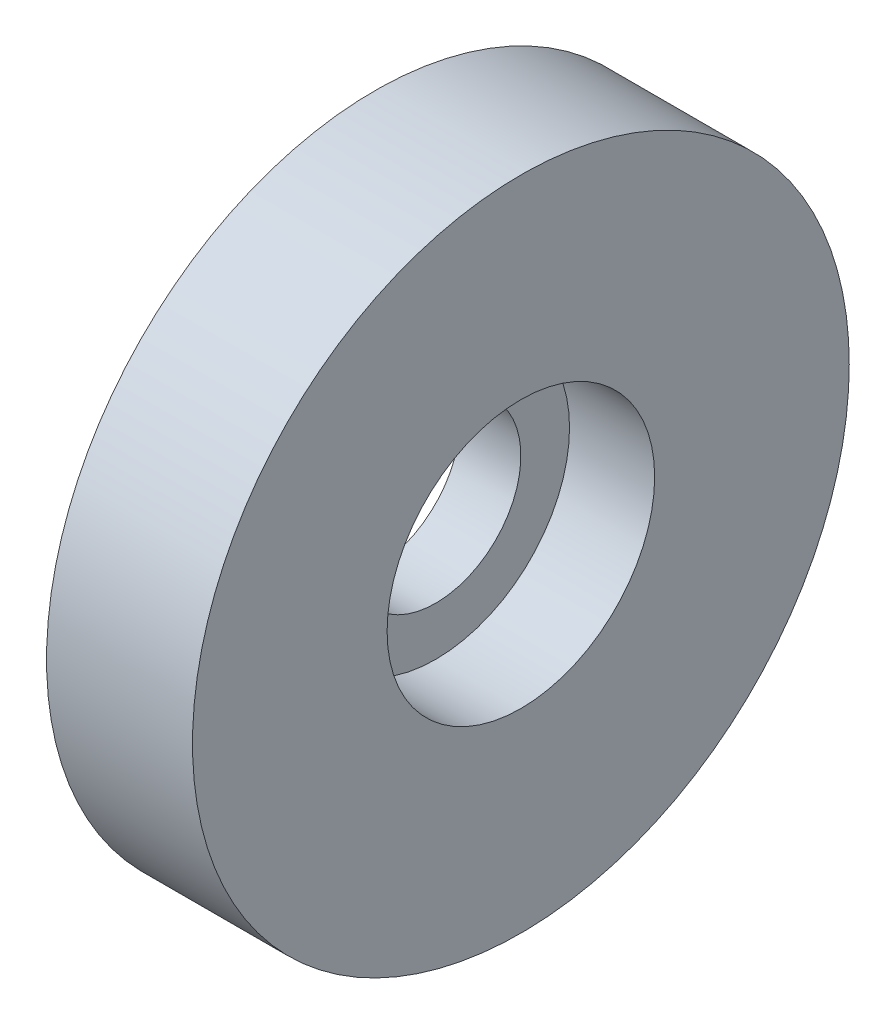
SolidWorks part; units mm, degrees
ref_plane "Front Plane" through (0, 0, 0) normal (0, 0, 1) x (1, 0, 0)
ref_plane "Top Plane" through (0, 0, 0) normal (0, 1, 0) x (1, 0, 0)
ref_plane "Right Plane" through (0, 0, 0) normal (1, 0, 0) x (0, 0, -1)
sketch "Sketch1" plane through (0, 0, 0) normal (0, 0, 1) x (1, 0, 0)
  line L0 (0, 0) -> (0, -12.5562) construction
  line L1 (-5, 0) -> (5, 0)
  line L2 (5, 0) -> (5, -4)
  line L3 (5, -4) -> (12, -4)
  line L4 (12, -4) -> (16.4979, -15.1251)
  line L5 (16.4979, -15.1251) -> (13, -20)
  line L6 (13, -20) -> (-13, -20)
  line L7 (-16.4979, -15.1251) -> (-13, -20)
  line L8 (-12, -4) -> (-16.4979, -15.1251)
  line L9 (-5, -4) -> (-12, -4)
  line L10 (-5, 0) -> (-5, -4)
  line L11 (0, 7) -> (15.343, 7) construction
  point P14 (0, -20)
  point P18 (0, 0)
  dimension "D1" = 5
  dimension "D2" = 7
  dimension "D3" = 4
  dimension "D4" = 12
  dimension "D5" = 6
  dimension "D6" = 13
  dimension "D7" = 20
  dimension "D8" = 7
revolve "Revolve1" add sketch "Sketch1" angle 360 about L11
ref_plane "Plane1" through (16.4979, 0, 0) normal (1, 0, 0) x (0, 0, -1)
other "SurfaceCut1"
ref_plane "Plane2" through (12, 0, 0) normal (1, 0, 0) x (0, 0, -1)
sketch "Sketch3" plane through (12, 0, 0) normal (1, 0, 0) x (0, 0, -1)
  line L1 (-30.8206, 37.7451) -> (28.7828, 37.7451)
  line L2 (-30.8206, 37.7451) -> (-30.8206, -21.8582)
  line L3 (-30.8206, -21.8582) -> (28.7828, -21.8582)
  line L4 (28.7828, 37.7451) -> (28.7828, -21.8582)
other "SurfaceCut4"
sketch "Sketch2" plane through (16.4979, 0, 0) normal (1, 0, 0) x (0, 0, -1)
  line L0 (0, 18.2899) -> (0, -18.2899) construction
  circle A0 centre (0, 7) radius 22.1251 construction
  circle A1 centre (0, 7) radius 22.1251 construction
  circle A2 centre (0, 25.5) radius 2.5
  circle A3 centre (0, 7) radius 11 construction
  circle A4 centre (0, 7) radius 11 construction
  circle A5 centre (6, 27.5) radius 2.5
  dimension "D1" = 5
  dimension "D2" = 5
  dimension "D3" = 5
  dimension "D4" = 6
  dimension "D5" = 2
extrude "Cut-Extrude1" cut sketch "Sketch2" against normal through all contours A5 | A2
pattern_circular "CirPattern1" count 10 over 360 about axis through (0, 7, 0) along (1, 0, 0)
